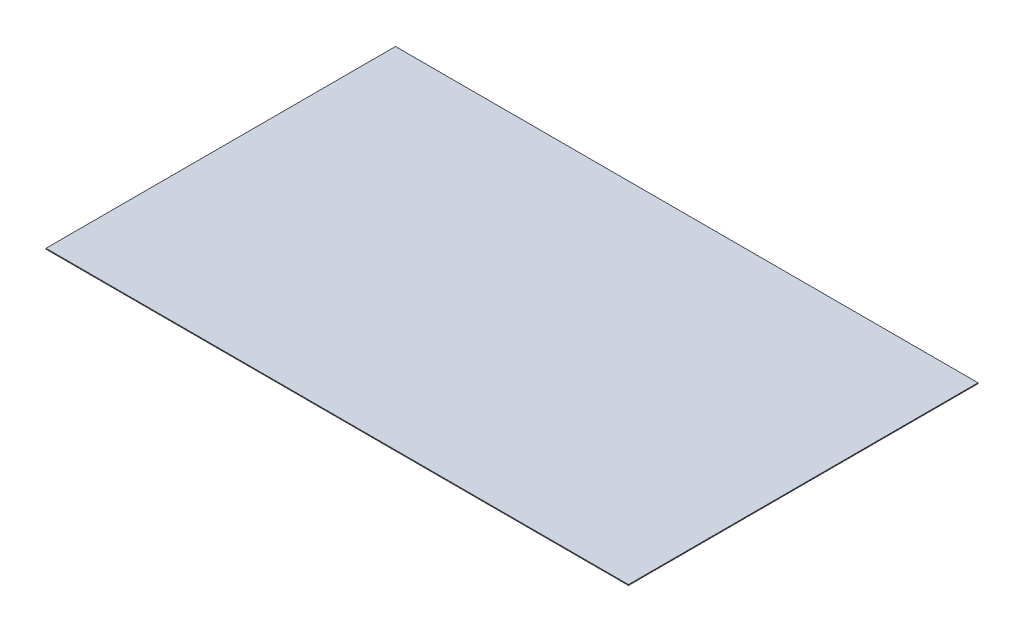
SolidWorks part; units mm, degrees
material "Copper"
ref_plane "Front Plane" through (0, 0, 0) normal (0, 0, 1) x (1, 0, 0)
ref_plane "Top Plane" through (0, 0, 0) normal (0, 1, 0) x (1, 0, 0)
ref_plane "Right Plane" through (0, 0, 0) normal (1, 0, 0) x (0, 0, -1)
sketch "Sketch1" plane through (0, 0, 0) normal (0, 1, 0) x (1, 0, 0)
  line L1 (0, 0) -> (25, 0)
  line L2 (0, 0) -> (0, 15)
  line L3 (0, 15) -> (25, 15)
  line L4 (25, 0) -> (25, 15)
  dimension "D1" = 15
  dimension "D2" = 25
extrude "Boss-Extrude1" add sketch "Sketch1" along normal blind 0.035
